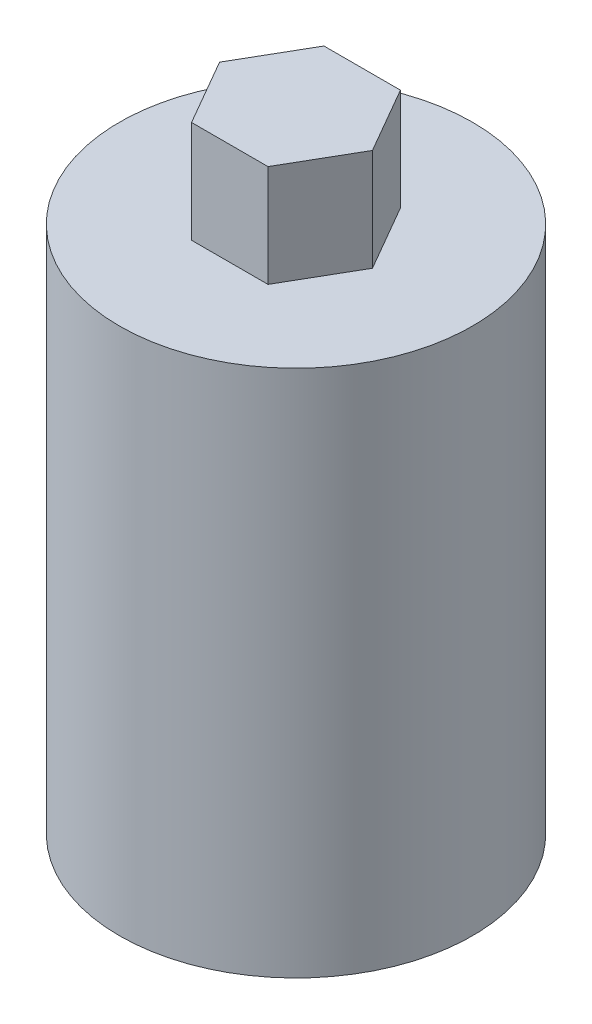
SolidWorks part; units mm, degrees
ref_plane "Front Plane" through (0, 0, 0) normal (0, 0, 1) x (1, 0, 0)
ref_plane "Top Plane" through (0, 0, 0) normal (0, 1, 0) x (1, 0, 0)
ref_plane "Right Plane" through (0, 0, 0) normal (1, 0, 0) x (0, 0, -1)
sketch "Sketch1" plane through (0, 0, 0) normal (0, 1, 0) x (1, 0, 0)
  circle A0 centre (0, 0) radius 3
  circle A1 centre (0, 0) radius 6.35
  dimension "D1" = 6
  dimension "D2" = 12.7
extrude "Boss-Extrude1" add sketch "Sketch1" along normal blind 12.5
sketch "Sketch4" plane through (0, 0, 0) normal (1, 0, 0) x (0, 0, -1)
  line L0 (6.35, 12.5) -> (-6.35, 12.5) construction
  circle A0 centre (0, 9.96) radius 2.413
  dimension "D1" = 4.826
  dimension "D2" = 2.54
extrude "Cut-Extrude1" cut sketch "Sketch4" against normal through all contours A0
sketch "Sketch6" plane through (0, 12.5, 0) normal (0, 1, 0) x (1, 0, 0)
  circle A0 centre (0, 0) radius 6.35
  dimension "D1" = 12.7
extrude "Boss-Extrude4" add sketch "Sketch6" along normal blind 6.4925
sketch "Sketch7" plane through (0, 18.9925, 0) normal (0, 1, 0) x (1, 0, 0)
  line L1 (-1.3748, 2.3812) -> (-2.7496, 0)
  line L2 (-2.7496, 0) -> (-1.3748, -2.3812)
  line L3 (-1.3748, -2.3812) -> (1.3748, -2.3812)
  line L4 (1.3748, -2.3812) -> (2.7496, 0)
  line L5 (2.7496, 0) -> (1.3748, 2.3812)
  line L6 (1.3748, 2.3812) -> (-1.3748, 2.3812)
  circle A0 centre (0, 0) radius 2.3812 construction
  dimension "D1" = 2.7496
  dimension "D2" = 2.7496
extrude "Boss-Extrude5" add sketch "Sketch7" along normal blind 3.67 contours L1 L2 L3 L4 L5 L6
